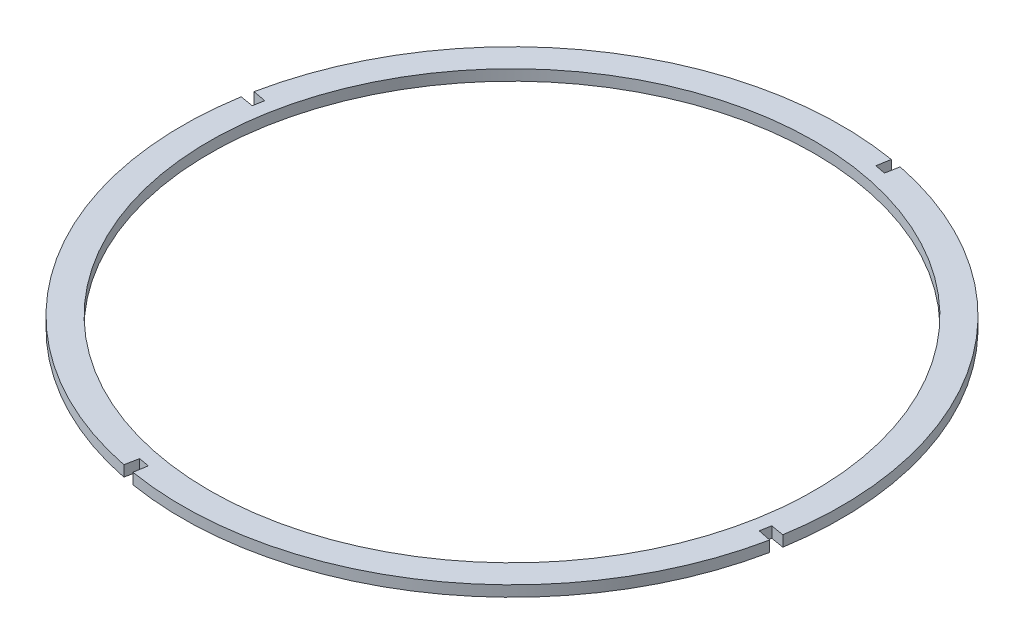
SolidWorks part; units mm, degrees
ref_plane "Спереди" through (0, 0, 0) normal (0, 0, 1) x (1, 0, 0)
ref_plane "Сверху" through (0, 0, 0) normal (0, 1, 0) x (1, 0, 0)
ref_plane "Справа" through (0, 0, 0) normal (1, 0, 0) x (0, 0, -1)
other "Configuration Table"
sketch "Эскиз1" plane through (0, 0, 0) normal (0, 1, 0) x (1, 0, 0)
  line L0 (-344.3291, 638.734) -> (-328.5946, 635.8313)
  line L1 (-421.4915, 176.36) -> (-336.4619, 637.2826) construction
  line L3 (-344.3291, 638.734) -> (-341.0482, 658.3938)
  line L4 (-328.5946, 635.8313) -> (-324.9782, 655.435)
  line L6 (-336.4619, 637.2826) -> (-506.2546, -284.6117) construction
  line L7 (-421.4915, 176.36) -> (39.4311, 91.3304) construction
  line L8 (-421.4915, 176.36) -> (-882.4141, 261.3896) construction
  line L9 (40.8824, 99.1977) -> (37.9798, 83.4632)
  line L10 (37.9798, 83.4632) -> (57.5162, 79.5132)
  line L11 (40.8824, 99.1977) -> (60.5423, 95.9168)
  line L12 (-514.1223, -283.1626) -> (-498.387, -286.0607)
  line L13 (-514.1223, -283.1626) -> (-518.0614, -302.7036)
  line L14 (-498.387, -286.0607) -> (-501.6561, -305.7202)
  line L15 (-880.9628, 269.2569) -> (-883.8654, 253.5224)
  line L16 (-880.9628, 269.2569) -> (-900.5665, 272.8733)
  line L17 (-883.8654, 253.5224) -> (-903.5253, 256.8033)
  arc A0 (-341.0482, 658.3938) -> (-900.5665, 272.8733) centre (-421.4915, 176.36) ccw
  circle A1 centre (-421.4915, 176.36) radius 448.7
  arc A2 (60.5423, 95.9168) -> (-324.9782, 655.435) centre (-421.4915, 176.36) ccw
  arc A3 (-501.6561, -305.7202) -> (57.5162, 79.5132) centre (-421.4915, 176.36) ccw
  arc A4 (-903.5253, 256.8033) -> (-518.0614, -302.7036) centre (-421.4915, 176.36) ccw
  point P7 (-336.4619, 637.2826)
  point P13 (-506.2546, -284.6117)
  point P16 (39.4311, 91.3304)
  point P24 (-882.4141, 261.3896)
  dimension "D1" = 977.4
  dimension "D2" = 897.4
  dimension "D3" = 0
  dimension "D4" = 0
  dimension "D5" = 16
  dimension "D6" = 16
  dimension "D7" = 0
  dimension "D8" = 468.7
  dimension "D9" = 16
  dimension "D10" = 0
  dimension "D11" = 16
  dimension "D12" = 0
  dimension "D13" = 468.7
  dimension "D14" = 468.7
  dimension "D15" = 468.7
  dimension "D16" = 0
extrude "Бобышка-Вытянуть2" add sketch "Эскиз1" along normal blind 16
